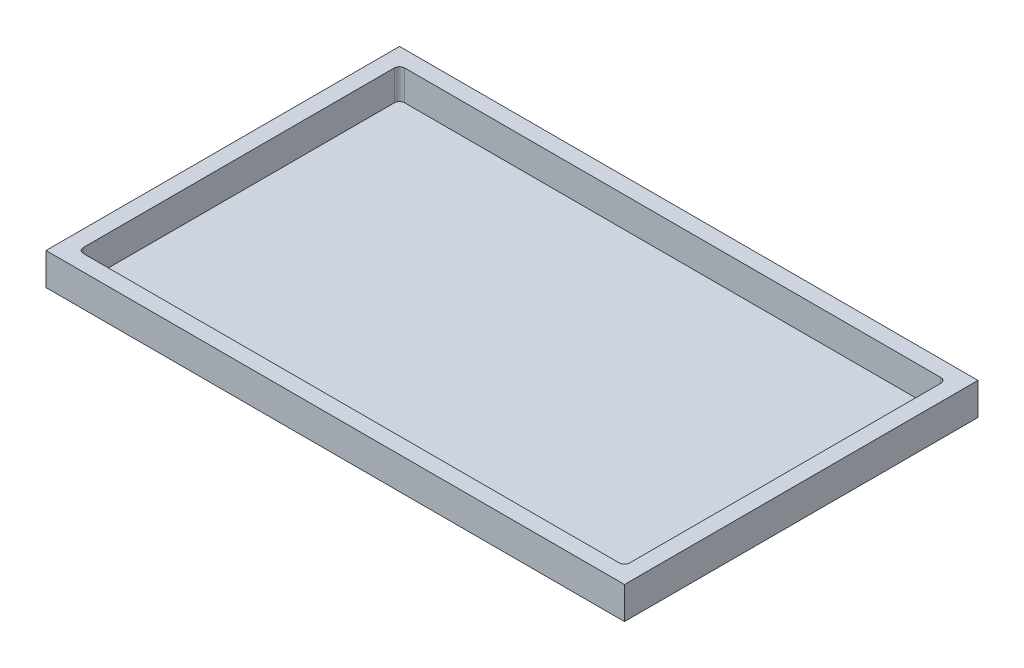
SolidWorks part; units mm, degrees
ref_plane "Ebene vorne" through (0, 0, 0) normal (0, 0, 1) x (1, 0, 0)
ref_plane "Ebene oben" through (0, 0, 0) normal (0, 1, 0) x (1, 0, 0)
ref_plane "Ebene rechts" through (0, 0, 0) normal (1, 0, 0) x (0, 0, -1)
sketch "Sketch1" plane through (0, 0, 0) normal (0, 1, 0) x (1, 0, 0)
  line L1 (-450, -275) -> (450, -275)
  line L2 (-450, -275) -> (-450, 275)
  line L3 (-450, 275) -> (450, 275)
  line L4 (450, -275) -> (450, 275)
  line L5 (-450, -275) -> (450, 275) construction
  line L6 (-450, 275) -> (450, -275) construction
  point P0 (0, 0)
  dimension "D1" = 550
  dimension "D2" = 900
extrude "Boss-Extrude1" add sketch "Sketch1" along normal blind 50
sketch "Sketch2" plane through (0, 50, 0) normal (0, 1, 0) x (1, 0, 0)
  line L1 (-425, -250) -> (425, -250)
  line L2 (-425, -250) -> (-425, 250)
  line L3 (-425, 250) -> (425, 250)
  line L4 (425, -250) -> (425, 250)
  line L5 (-425, -250) -> (425, 250) construction
  line L6 (-425, 250) -> (425, -250) construction
  point P0 (0, 0)
  dimension "D1" = 500
  dimension "D2" = 850
extrude "Cut-Extrude1" cut sketch "Sketch2" against normal blind 47 contours L2 L3 L4 L1
sketch "Sketch3" plane through (0, 3, 0) normal (0, 1, 0) x (1, 0, 0)
  line L0 (-425, 250) -> (-395, 250)
  line L1 (-425, 250) -> (425, 250) construction
  line L2 (-425, 250) -> (-425, 220)
  line L3 (-425, -250) -> (-425, 250) construction
  line L4 (-425, 220) -> (-395, 250)
extrude "Boss-Extrude2" [suppressed] add sketch "Sketch3" along normal blind 34 contours L4 L0 L2
mirror "Mirror1" [suppressed] about plane through (0, 0, 0) normal (0, 0, 1)
mirror "Mirror2" [suppressed] about plane through (0, 0, 0) normal (1, 0, 0)
fillet "Fillet1" radius 8 4 edges at (-425, 26.5, 250) (-425, 26.5, -250) (425, 26.5, -250) (425, 26.5, 250)
